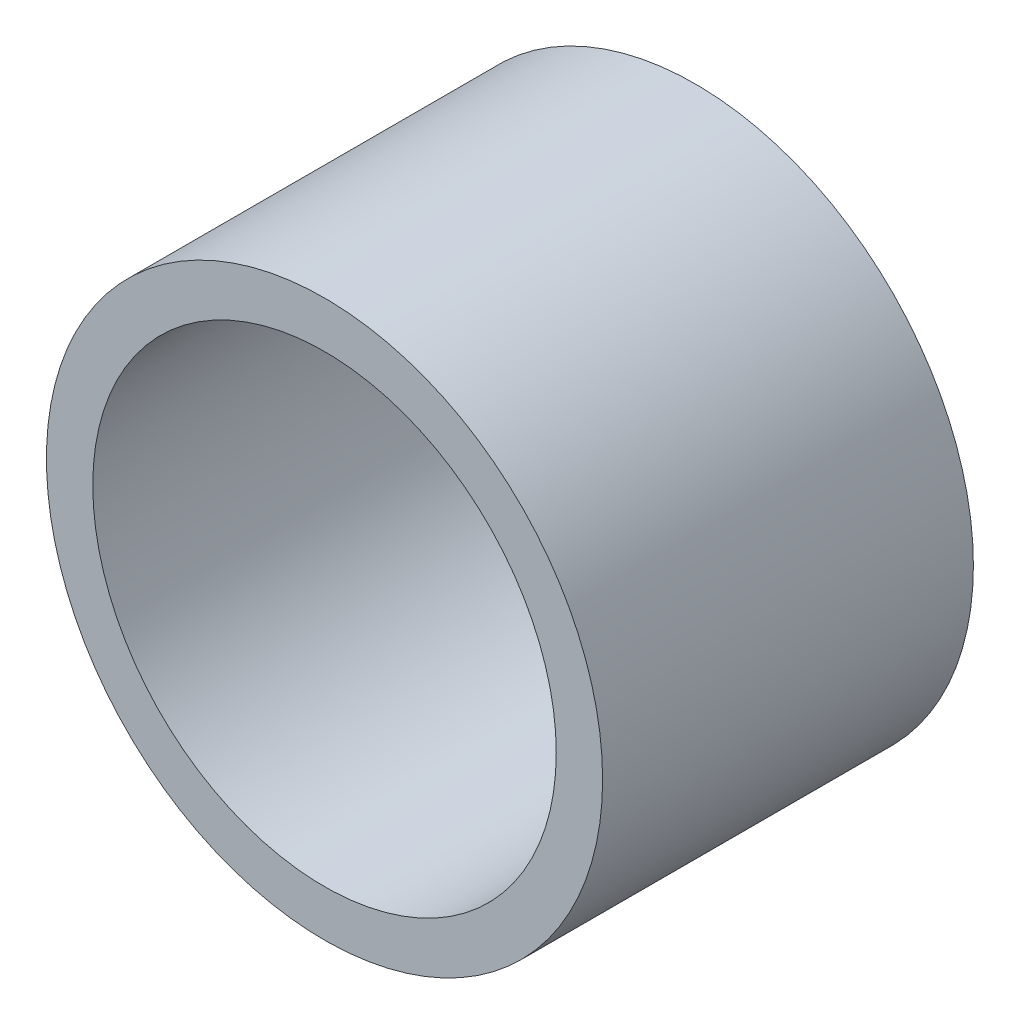
SolidWorks part; units mm, degrees
material "AISI 4130 Steel, normalized at 870C"
ref_plane "Front Plane" through (0, 0, 0) normal (0, 0, 1) x (1, 0, 0)
ref_plane "Top Plane" through (0, 0, 0) normal (0, 1, 0) x (1, 0, 0)
ref_plane "Right Plane" through (0, 0, 0) normal (1, 0, 0) x (0, 0, -1)
sketch "Sketch1" plane through (0, 0, 0) normal (0, 0, 1) x (1, 0, 0)
  circle A0 centre (0, 0) radius 15.875
  circle A1 centre (0, 0) radius 19.05
  dimension "D1" = 31.75
  dimension "D2" = 38.1
extrude "Housing" add sketch "Sketch1" along normal blind 25.4
